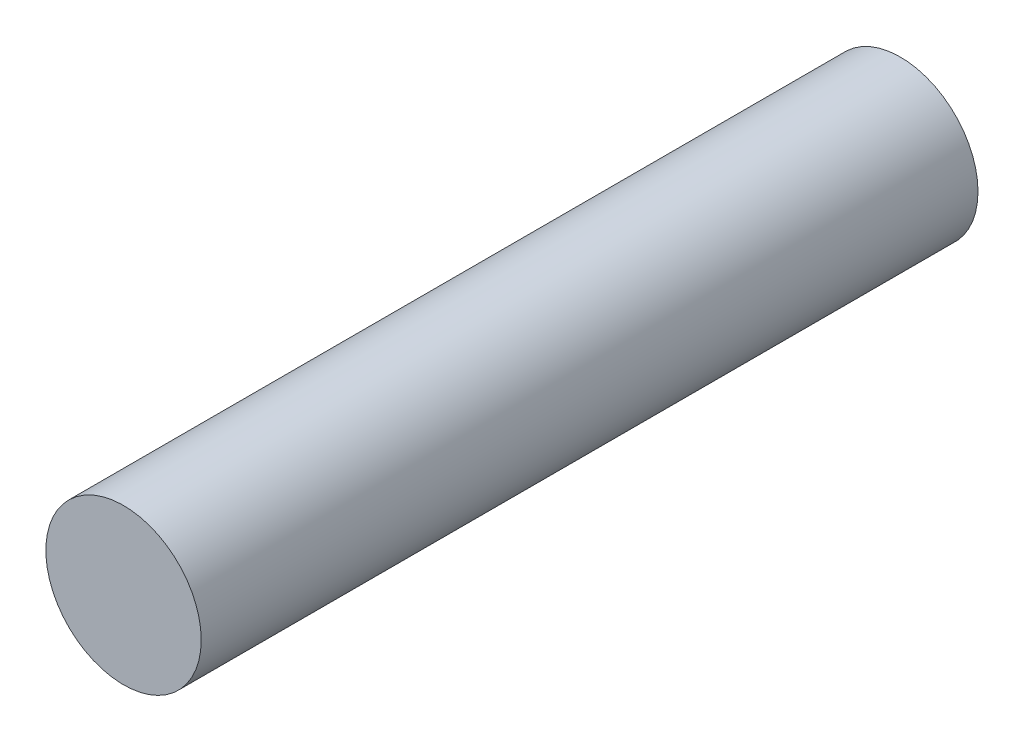
SolidWorks part; units mm, degrees
ref_plane "Plano frontal" through (0, 0, 0) normal (0, 0, 1) x (1, 0, 0)
ref_plane "Plano superior" through (0, 0, 0) normal (0, 1, 0) x (1, 0, 0)
ref_plane "Plano direito" through (0, 0, 0) normal (1, 0, 0) x (0, 0, -1)
sketch "Esboço1" plane through (0, 0, 0) normal (0, 0, 1) x (1, 0, 0)
  circle A0 centre (0, 0) radius 5
  dimension "D1" = 10
extrude "Ressalto-extrusão1" add sketch "Esboço1" along normal blind 50
